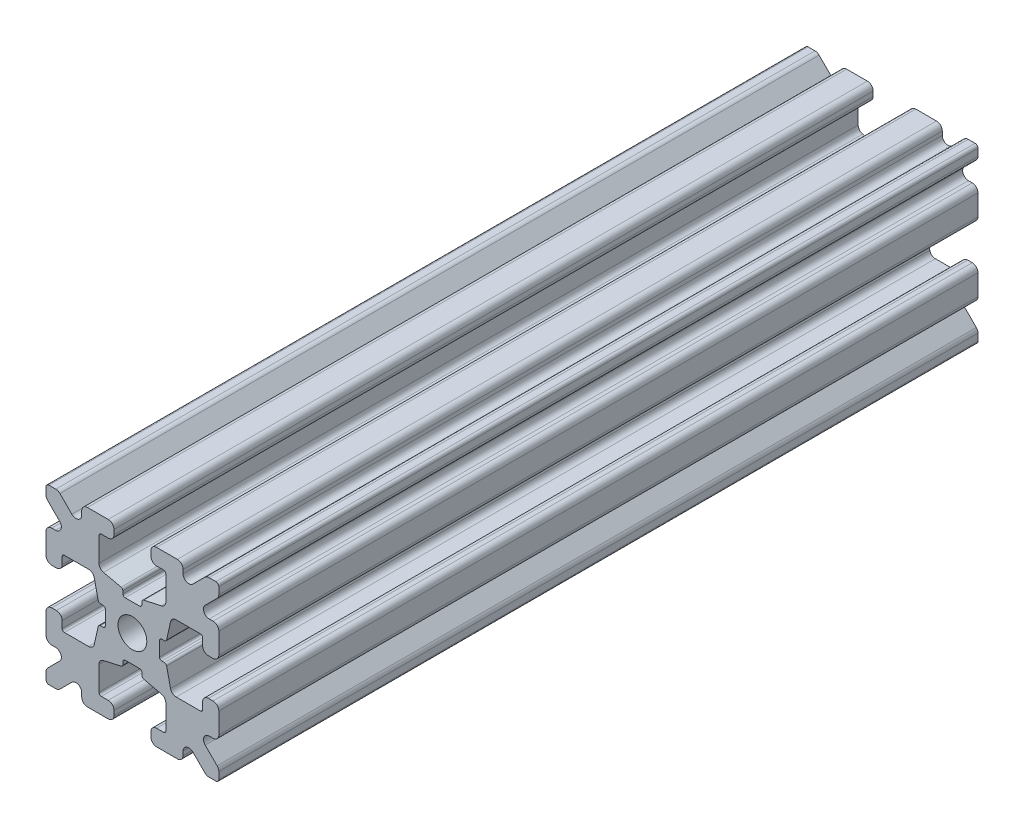
SolidWorks part; units mm, degrees
ref_plane "Front Plane" through (0, 0, 0) normal (0, 0, 1) x (1, 0, 0)
ref_plane "Top Plane" through (0, 0, 0) normal (0, 1, 0) x (1, 0, 0)
ref_plane "Right Plane" through (0, 0, 0) normal (1, 0, 0) x (0, 0, -1)
sketch "Sketch1" plane through (0, 0, 0) normal (0, 0, 1) x (1, 0, 0)
  line L1 (-7.5, -7.5) -> (7.5, -7.5)
  line L2 (-7.5, -7.5) -> (-7.5, 7.5)
  line L3 (-7.5, 7.5) -> (7.5, 7.5)
  line L4 (7.5, -7.5) -> (7.5, 7.5)
  line L5 (-7.5, -7.5) -> (7.5, 7.5) construction
  line L6 (-7.5, 7.5) -> (7.5, -7.5) construction
  circle A0 centre (0, 0) radius 1.25
  point P0 (0, 0)
  dimension "D2" = 2.5
  dimension "D1" = 15
extrude "Boss-Extrude1" add sketch "Sketch1" along normal mid plane 65.9
fillet "Fillet1" radius 0.25 4 edges at (7.5, -7.5, 0) (-7.5, -7.5, 0) (7.5, 7.5, 0) (-7.5, 7.5, 0)
sketch "Sketch2" plane through (0, 0, 32.95) normal (0, 0, 1) x (1, 0, 0)
  line L0 (-7.5, 7.25) -> (-7.5, -7.25) construction
  line L1 (-7.5, 1.6) -> (-6.1, 1.6)
  line L2 (-7.5, 1.6) -> (-7.5, -1.6)
  line L3 (-7.5, -1.6) -> (-6.1, -1.6)
  line L4 (-6.1, 1.6) -> (-6.1, 2.9)
  line L5 (0, 0) -> (-12.1036, 0) construction
  line L6 (-6.1, -2.9) -> (-3.4, -2.9)
  line L7 (0, 0) -> (-7.25, 7.25) construction
  line L8 (-6.1, 2.9) -> (-3.4, 2.9)
  line L9 (-3.4, -2.9) -> (-3.4, 2.9)
  line L10 (55, 0) -> (-55, 0) construction
  line L11 (-6.1, -2.9) -> (-6.1, -1.6)
  line L12 (2.9, 6.1) -> (1.6, 6.1)
  line L13 (2.9, 3.4) -> (-2.9, 3.4)
  line L14 (-2.9, 6.1) -> (-2.9, 3.4)
  line L15 (2.9, 6.1) -> (2.9, 3.4)
  line L16 (-1.6, 6.1) -> (-2.9, 6.1)
  line L17 (1.6, 7.5) -> (1.6, 6.1)
  line L18 (-1.6, 7.5) -> (1.6, 7.5)
  line L19 (-1.6, 7.5) -> (-1.6, 6.1)
  line L20 (-1.6, -7.5) -> (-1.6, -6.1)
  line L21 (-1.6, -7.5) -> (1.6, -7.5)
  line L22 (1.6, -7.5) -> (1.6, -6.1)
  line L23 (-1.6, -6.1) -> (-2.9, -6.1)
  line L24 (2.9, -6.1) -> (2.9, -3.4)
  line L25 (-2.9, -6.1) -> (-2.9, -3.4)
  line L26 (2.9, -3.4) -> (-2.9, -3.4)
  line L27 (2.9, -6.1) -> (1.6, -6.1)
  line L28 (6.1, -2.9) -> (6.1, -1.6)
  line L29 (3.4, -2.9) -> (3.4, 2.9)
  line L30 (6.1, 2.9) -> (3.4, 2.9)
  line L31 (6.1, -2.9) -> (3.4, -2.9)
  line L32 (6.1, 1.6) -> (6.1, 2.9)
  line L33 (7.5, -1.6) -> (6.1, -1.6)
  line L34 (7.5, 1.6) -> (7.5, -1.6)
  line L35 (7.5, 1.6) -> (6.1, 1.6)
  dimension "D1" = 3.2
  dimension "D2" = 5.8
  dimension "D3" = 1.4
  dimension "D4" = 2.7
extrude "Cut-Extrude1" cut sketch "Sketch2" against normal through all
sketch "Sketch4" plane through (0, 0, 32.95) normal (0, 0, 1) x (1, 0, 0)
  line L0 (-3.4, 2.9) -> (-2.75, 0)
  line L1 (55, 0) -> (-55, 0) construction
  line L2 (-2.75, 0) -> (-3.4, -2.9)
  line L3 (-3.4, -2.9) -> (-3.4, 2.9) construction
  line L4 (-3.4, 2.9) -> (-3.4, -2.9)
  line L5 (-2.9, 3.4) -> (0, 2.75)
  line L6 (0, 2.75) -> (2.9, 3.4)
  line L7 (2.9, 3.4) -> (-2.9, 3.4)
  line L8 (3.4, 2.9) -> (2.75, 0)
  line L9 (2.75, 0) -> (3.4, -2.9)
  line L10 (3.4, -2.9) -> (3.4, 2.9)
  line L11 (-2.9, -3.4) -> (0, -2.75)
  line L12 (0, -2.75) -> (2.9, -3.4)
  line L13 (2.9, -3.4) -> (-2.9, -3.4)
  circle A2 centre (0, 0) radius 2.75
  circle A3 centre (0, 0) radius 2.75 construction
  dimension "D1" = 1.5
extrude "Cut-Extrude3" cut sketch "Sketch4" against normal through all
fillet "Fillet3" radius 0.5 16 edges at (-6.1, -1.6, 0) (-7.5, -1.6, 0) (-6.1, 1.6, 0) (-7.5, 1.6, 0) (-1.6, -7.5, 0) (-1.6, -6.1, 0) (1.6, -7.5, 0) (1.6, -6.1, 0) (6.1, -1.6, 0) (7.5, -1.6, 0) (7.5, 1.6, 0) (6.1, 1.6, 0) (1.6, 7.5, 0) (1.6, 6.1, 0) (-1.6, 7.5, 0) (-1.6, 6.1, 0)
fillet "Fillet4" radius 0.5 8 edges at (-3.4, 2.9, 0) (-3.4, -2.9, 0) (2.9, -3.4, 0) (-2.9, -3.4, 0) (3.4, -2.9, 0) (3.4, 2.9, 0) (-2.9, 3.4, 0) (2.9, 3.4, 0)
fillet "Fillet5" radius 3 4 edges at (0, -2.75, 0) (2.75, 0, 0) (-2.75, 0, 0) (0, 2.75, 0)
fillet "Fillet6" radius 0.2 8 edges at (-2.9, -6.1, 0) (2.9, -6.1, 0) (6.1, -2.9, 0) (6.1, 2.9, 0) (2.9, 6.1, 0) (-2.9, 6.1, 0) (-6.1, -2.9, 0) (-6.1, 2.9, 0)
sketch "Sketch5" plane through (0, 0, 32.95) normal (0, 0, 1) x (1, 0, 0)
  line L0 (0, 0) -> (-7.25, 7.25) construction
  line L1 (-7.5, 6.4393) -> (-5.4607, 4.4)
  line L2 (-6.4393, 7.5) -> (-4.4, 5.4607)
  line L3 (-7.5, 4.4) -> (-5.4607, 4.4)
  line L4 (-3.8003, 2.9) -> (-5.9, 2.9) construction
  line L5 (0, 0) -> (-12.1819, 0) construction
  line L6 (-4.4, 7.5) -> (-4.4, 5.4607)
  line L7 (-2.9, 5.9) -> (-2.9, 3.8003) construction
  line L8 (-7.5, 6.4393) -> (-7.5, 4.4)
  line L9 (-7.5, 7.25) -> (-7.5, 2.1) construction
  line L10 (2.1, -7.5) -> (7.25, -7.5) construction
  line L11 (7.5, -7.25) -> (7.5, -2.1) construction
  line L12 (7.25, 7.5) -> (2.1, 7.5) construction
  line L13 (-2.1, 7.5) -> (-7.25, 7.5) construction
  line L14 (-4.4, 7.5) -> (-6.4393, 7.5)
  line L16 (55, 0) -> (-55, 0) construction
  line L17 (0, 0) -> (0, 10.993) construction
  line L18 (0, -54.6431) -> (0, 54.6431) construction
  line L20 (4.4, 7.5) -> (6.4393, 7.5)
  line L22 (7.5, 6.4393) -> (7.5, 4.4)
  line L23 (4.4, 7.5) -> (4.4, 5.4607)
  line L24 (7.5, 4.4) -> (5.4607, 4.4)
  line L25 (6.4393, 7.5) -> (4.4, 5.4607)
  line L26 (7.5, 6.4393) -> (5.4607, 4.4)
  line L27 (7.5, -6.4393) -> (5.4607, -4.4)
  line L28 (6.4393, -7.5) -> (4.4, -5.4607)
  line L29 (7.5, -4.4) -> (5.4607, -4.4)
  line L30 (4.4, -7.5) -> (4.4, -5.4607)
  line L31 (7.5, -6.4393) -> (7.5, -4.4)
  line L33 (4.4, -7.5) -> (6.4393, -7.5)
  line L36 (-4.4, -7.5) -> (-6.4393, -7.5)
  line L38 (-7.5, -6.4393) -> (-7.5, -4.4)
  line L39 (-4.4, -7.5) -> (-4.4, -5.4607)
  line L40 (-7.5, -4.4) -> (-5.4607, -4.4)
  line L41 (-6.4393, -7.5) -> (-4.4, -5.4607)
  line L42 (-7.5, -6.4393) -> (-5.4607, -4.4)
  dimension "D1" = 1.5
  dimension "D2" = 1.5
  dimension "D3" = 1.5
extrude "Cut-Extrude4" cut sketch "Sketch5" against normal through all
fillet "Fillet8" radius 0.5 24 edges at (-5.4607, 4.4, 0) (-7.5, 4.4, 0) (-5.4607, -4.4, 0) (-7.5, -4.4, 0) (-4.4, -7.5, 0) (-4.4, -5.4607, 0) (4.4, -7.5, 0) (4.4, -5.4607, 0) (5.4607, -4.4, 0) (7.5, -4.4, 0) (7.5, 4.4, 0) (5.4607, 4.4, 0) (4.4, 5.4607, 0) (4.4, 7.5, 0) (-4.4, 5.4607, 0) (-4.4, 7.5, 0) (-6.4393, 7.5, 0) (-7.5, 6.4393, 0) (6.4393, 7.5, 0) (7.5, 6.4393, 0) (6.4393, -7.5, 0) (7.5, -6.4393, 0) (-6.4393, -7.5, 0) (-7.5, -6.4393, 0)
sketch "Sketch6" plane through (0, 0, 32.95) normal (0, 0, 1) x (1, 0, 0)
  line L0 (0, 0) -> (0, 11.013) construction
  line L1 (0.6561, 2.8971) -> (2.1235, 2.8971) construction
  line L2 (0, -54.6431) -> (0, 54.6431) construction
  line L3 (0, 0) -> (7.25, 7.25) construction
  line L4 (7.5, 0.8255) -> (7.5, -0.8255)
  line L5 (2.3471, 0.8255) -> (7.5, 0.8255)
  line L6 (0, 0) -> (12.4016, 0) construction
  line L7 (0.8255, -7.5) -> (-0.8255, -7.5)
  line L8 (2.3471, -0.8255) -> (2.3471, 0.8255)
  line L9 (0.8255, -2.3471) -> (0.8255, -7.5)
  line L10 (7.5, -0.8255) -> (2.3471, -0.8255)
  line L11 (-7.5, -0.8255) -> (-2.3471, -0.8255)
  line L12 (-2.3471, -0.8255) -> (-2.3471, 0.8255)
  line L13 (-0.8255, -2.3471) -> (0.8255, -2.3471)
  line L14 (-0.8255, 7.5) -> (-0.8255, 2.3471)
  line L15 (-0.8255, 2.3471) -> (0.8255, 2.3471)
  line L16 (-0.8255, -7.5) -> (-0.8255, -2.3471)
  line L17 (0.8255, 2.3471) -> (0.8255, 7.5)
  line L18 (0.8255, 7.5) -> (-0.8255, 7.5)
  line L19 (3.9, 7.5) -> (2.1, 7.5) construction
  line L20 (-2.3471, 0.8255) -> (-7.5, 0.8255)
  line L21 (-7.5, 0.8255) -> (-7.5, -0.8255)
  point P5 (0, -2.5973)
  point P7 (0, 2.5973)
  dimension "D3" = 0.55
  dimension "D1" = 1.651
extrude "Cut-Extrude5" cut sketch "Sketch6" against normal through all
fillet "Fillet10" radius 0.2 16 edges at (-2.935, 0.8255, 0) (-2.935, -0.8255, 0) (2.935, -0.8255, 0) (2.935, 0.8255, 0) (0.8255, 2.935, 0) (-0.8255, 2.935, 0) (-2.3471, 0.8255, 0) (-2.3471, -0.8255, 0) (0.8255, 2.3471, 0) (-0.8255, 2.3471, 0) (2.3471, 0.8255, 0) (2.3471, -0.8255, 0) (0.8255, -2.935, 0) (0.8255, -2.3471, 0) (-0.8255, -2.3471, 0) (-0.8255, -2.935, 0)
